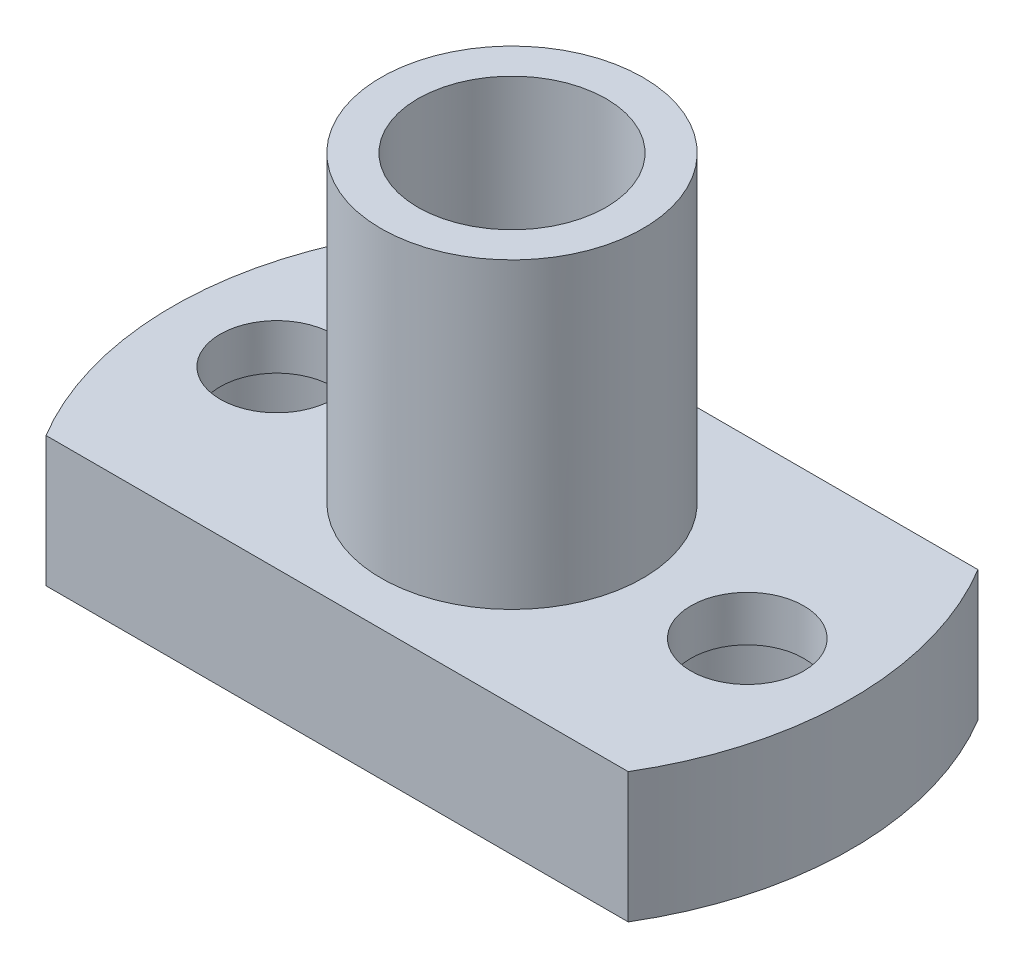
SolidWorks part; units mm, degrees
ref_plane "Front Plane" through (0, 0, 0) normal (0, 0, 1) x (1, 0, 0)
ref_plane "Top Plane" through (0, 0, 0) normal (0, 1, 0) x (1, 0, 0)
ref_plane "Right Plane" through (0, 0, 0) normal (1, 0, 0) x (0, 0, -1)
sketch "Sketch1" plane through (0, 0, 0) normal (0, 1, 0) x (1, 0, 0)
  line L0 (0, 5.575) -> (0, -5.575) construction
  line L1 (-9.279, -5.575) -> (9.279, -5.575)
  line L2 (-9.279, -5.575) -> (-9.279, 5.575) construction
  line L3 (-9.279, 5.575) -> (9.279, 5.575)
  line L4 (9.279, -5.575) -> (9.279, 5.575) construction
  line L5 (-9.279, -5.575) -> (9.279, 5.575) construction
  line L6 (-9.279, 5.575) -> (9.279, -5.575) construction
  line L7 (-10.825, 0) -> (10.825, 0) construction
  arc A0 (-9.279, 5.575) -> (-9.279, -5.575) centre (0, 0) ccw
  arc A1 (9.279, 5.575) -> (9.279, -5.575) centre (0, 0) cw
  circle A2 centre (-7.5, 0) radius 1.8
  circle A3 centre (7.5, 0) radius 1.8
  circle A5 centre (0, 0) radius 3
  point P0 (0, 0)
  point P16 (14.123, 0)
  point P18 (0, 0)
  dimension "D3" = 10.825
  dimension "D4" = 15
  dimension "D5" = 3.6
  dimension "D6" = 6
  dimension "D2" = 11.15
extrude "Boss-Extrude1" add sketch "Sketch1" along normal blind 4.15
sketch "Sketch2" plane through (0, 4.15, 0) normal (0, 1, 0) x (1, 0, 0)
  circle A0 centre (0, 0) radius 4.175
  circle A1 centre (0, 0) radius 3
  circle A2 centre (0, 0) radius 3 construction
  dimension "D1" = 8.35
extrude "Boss-Extrude2" add sketch "Sketch2" along normal blind 9.65
sketch "Sketch3" plane through (0, 0, 0) normal (0, -1, 0) x (1, 0, 0)
  circle A0 centre (7.5, 0) radius 3
  circle A1 centre (-7.5, 0) radius 3
  circle A2 centre (-7.5, 0) radius 1.8 construction
  point P5 (-7.6151, 0)
  dimension "D1" = 6
extrude "Cut-Extrude1" cut sketch "Sketch3" against normal blind 2.7
